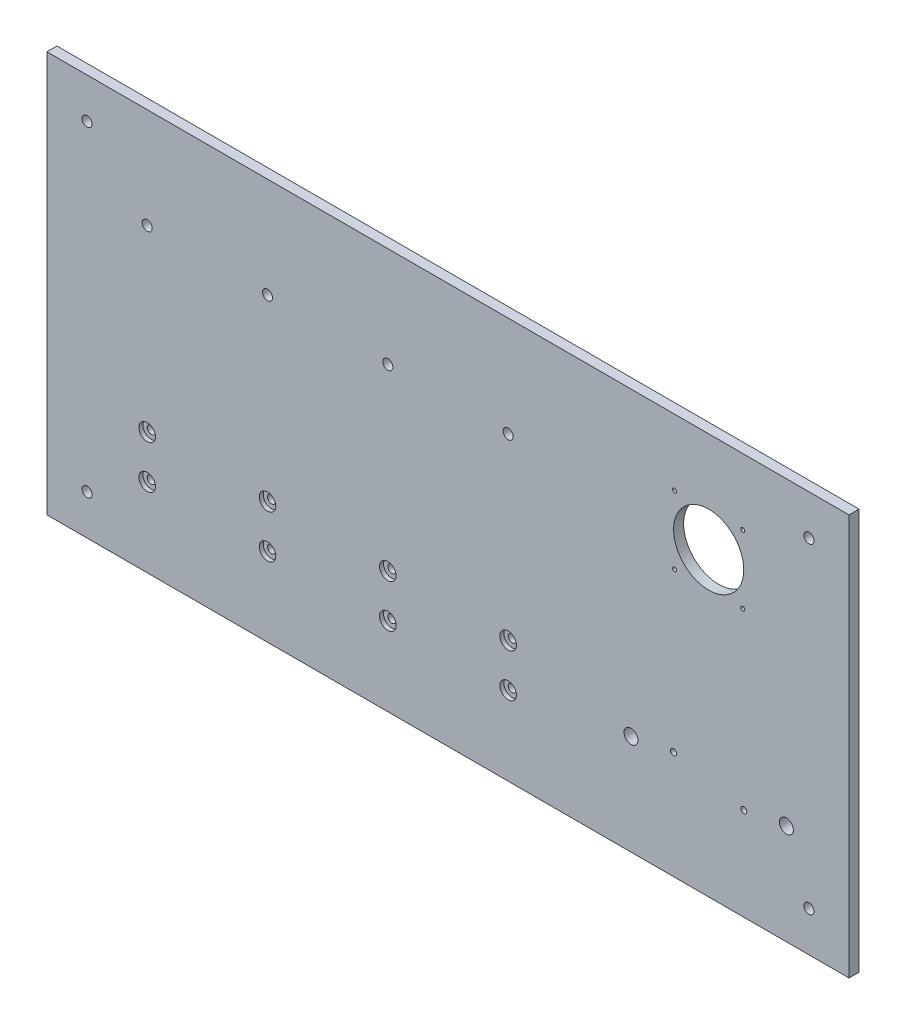
SolidWorks part; units mm, degrees
ref_plane "Спереди" through (0, 0, 0) normal (0, 0, 1) x (1, 0, 0)
ref_plane "Сверху" through (0, 0, 0) normal (0, 1, 0) x (1, 0, 0)
ref_plane "Справа" through (0, 0, 0) normal (1, 0, 0) x (0, 0, -1)
sketch "Эскиз1" plane through (0, 0, 0) normal (0, 0, 1) x (1, 0, 0)
  line L0 (0, 300) -> (800, 300) construction
  line L1 (800, 400) -> (0, 400)
  line L2 (800, 400) -> (800, 0)
  line L3 (800, 0) -> (0, 0)
  line L4 (0, 400) -> (0, 0)
  line L5 (660, 334) -> (660, 266) construction
  line L6 (626, 334) -> (694, 334) construction
  line L7 (626, 334) -> (626, 266) construction
  line L8 (626, 266) -> (694, 266) construction
  line L9 (694, 334) -> (694, 266) construction
  line L10 (0, 78.5) -> (800, 78.5) construction
  line L11 (582.5, 121.5) -> (582.5, 78.5) construction
  line L12 (0, 121.5) -> (800, 121.5) construction
  line L13 (100, 300) -> (100, 78.5) construction
  line L14 (660, 266) -> (660, 100) construction
  line L15 (220, 300) -> (220, 78.5) construction
  line L16 (737.5, 121.5) -> (737.5, 78.5) construction
  line L17 (340, 300) -> (340, 78.5) construction
  line L18 (625, 107.5) -> (625, 100) construction
  line L19 (460, 300) -> (460, 78.5) construction
  line L20 (582.5, 100) -> (737.5, 100) construction
  line L21 (40, 400) -> (40, 0) construction
  line L22 (695, 92.5) -> (695, 100) construction
  line L23 (40, 360) -> (760, 360) construction
  line L24 (760, 400) -> (760, 0) construction
  line L28 (40, 40) -> (760, 40) construction
  circle A0 centre (660, 300) radius 35
  circle A1 centre (626, 334) radius 2
  circle A2 centre (694, 334) radius 2
  circle A3 centre (694, 266) radius 2
  circle A4 centre (626, 266) radius 2
  circle A5 centre (100, 300) radius 5
  circle A6 centre (220, 300) radius 5
  circle A7 centre (340, 300) radius 5
  circle A8 centre (460, 300) radius 5
  circle A9 centre (100, 121.5) radius 4
  circle A10 centre (220, 121.5) radius 4
  circle A11 centre (340, 121.5) radius 4
  circle A12 centre (460, 121.5) radius 4
  circle A13 centre (460, 78.5) radius 4
  circle A14 centre (340, 78.5) radius 4
  circle A15 centre (220, 78.5) radius 4
  circle A16 centre (100, 78.5) radius 4
  circle A17 centre (582.5, 100) radius 7
  circle A18 centre (737.5, 100) radius 7
  circle A19 centre (625, 107.5) radius 3
  circle A20 centre (695, 92.5) radius 3
  circle A21 centre (40, 360) radius 5
  circle A22 centre (760, 360) radius 5
  circle A23 centre (760, 40) radius 5
  circle A24 centre (40, 40) radius 5
  point P58 (625, 103.75)
  dimension "D4" = 70
  dimension "D5" = 4
  dimension "D6" = 10
  dimension "D11" = 8
  dimension "D13" = 14
  dimension "D18" = 6
  dimension "D27" = 10
  dimension "D1" = 400
  dimension "D2" = 800
  dimension "D3" = 68
  dimension "D7" = 120
  dimension "D8" = 120
  dimension "D9" = 120
  dimension "D10" = 43
  dimension "D12" = 155
  dimension "D14" = 7.5
  dimension "D15" = 7.5
  dimension "D16" = 70
  dimension "D17" = 35
  dimension "D19" = 200
  dimension "D20" = 100
  dimension "D21" = 200
  dimension "D22" = 100
  dimension "D23" = 40
  dimension "D24" = 40
  dimension "D25" = 40
  dimension "D26" = 40
extrude "Бобышка-Вытянуть1" add sketch "Эскиз1" along normal blind 10
sketch "Эскиз2" plane through (0, 0, 10) normal (0, 0, 1) x (1, 0, 0)
  circle A0 centre (100, 121.5) radius 8.25
  circle A1 centre (100, 78.5) radius 8.25
  circle A2 centre (220, 121.5) radius 8.25
  circle A3 centre (220, 78.5) radius 8.25
  circle A4 centre (340, 121.5) radius 8.25
  circle A5 centre (460, 121.5) radius 8.25
  circle A6 centre (460, 78.5) radius 8.25
  circle A7 centre (340, 78.5) radius 8.25
  dimension "D1" = 16.5
extrude "Вырез-Вытянуть1" cut sketch "Эскиз2" against normal blind 4
